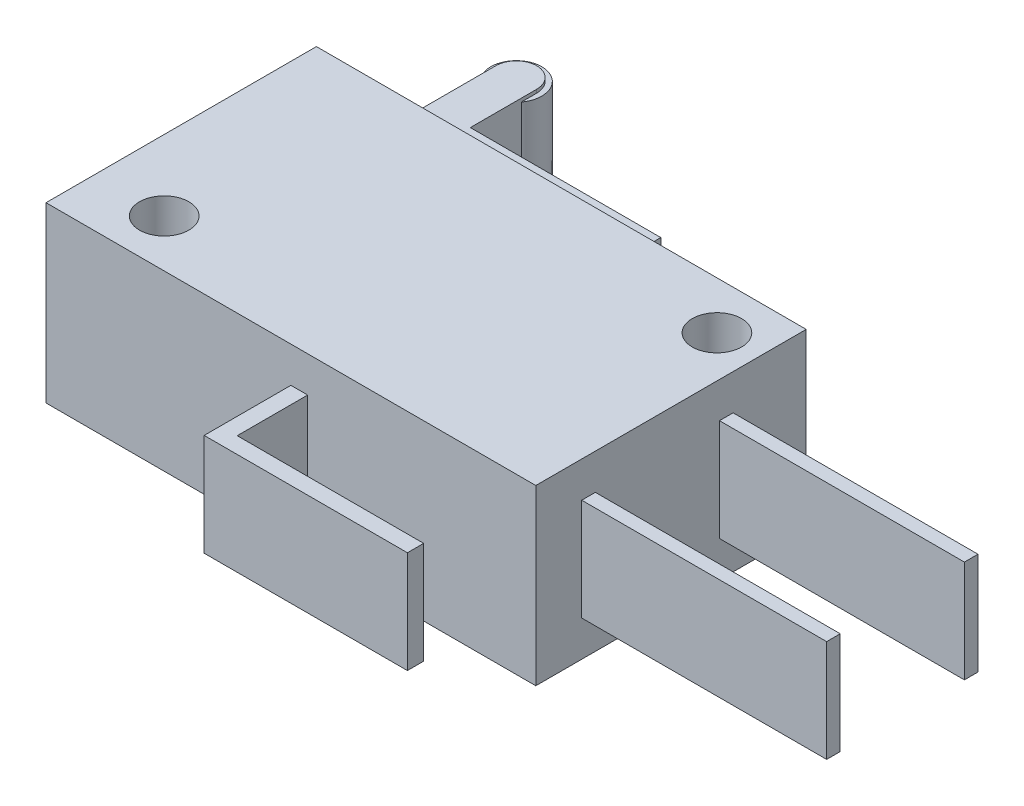
SolidWorks part; units mm, degrees
ref_plane "Front Plane" through (0, 0, 0) normal (0, 0, 1) x (1, 0, 0)
ref_plane "Top Plane" through (0, 0, 0) normal (0, 1, 0) x (1, 0, 0)
ref_plane "Right Plane" through (0, 0, 0) normal (1, 0, 0) x (0, 0, -1)
sketch "Sketch1" plane through (0, 0, 0) normal (0, 1, 0) x (1, 0, 0)
  line L5 (-14.4, -7.95) -> (14.4, -7.95)
  line L6 (-14.4, -7.95) -> (-14.4, 7.95)
  line L11 (-14.4, 7.95) -> (14.4, 7.95)
  line L12 (14.4, -7.95) -> (14.4, 7.95)
  line L13 (0, 7.95) -> (0, -7.95) construction
  line L14 (-14.4, 0) -> (14.4, 0) construction
  point P0 (0, 0)
  point P1 (0, 0)
  point P5 (0, 0)
extrude "Boss-Extrude2" add sketch "Sketch1" along normal blind 10.2
sketch "Sketch3" plane through (0, 10.2, 0) normal (0, 1, 0) x (1, 0, 0)
  line L2 (-14.4, 7.95) -> (14.4, 7.95) construction
  line L5 (14.4, -7.95) -> (14.4, 7.95) construction
  circle A0 centre (11.95, 5.15) radius 1.45
  circle A1 centre (-10.25, -5.15) radius 1.45
  point P6 (-10.3976, -4.112)
  dimension "D2" = 22.2
  dimension "D3" = 2.9
  dimension "D4" = 2.9
  dimension "D5" = 10.3
  dimension "D6" = 2.45
  dimension "D1" = 2.8
extrude "Cut-Extrude1" cut sketch "Sketch3" against normal blind 17.45
ref_plane "Plane1" through (0, 5.1, 0) normal (0, 1, 0) x (1, 0, 0)
sketch "Sketch7" plane through (0, 5.1, 0) normal (0, 1, 0) x (1, 0, 0)
  line L0 (-10.25, -5.15) -> (-10.25, 15.45) construction
  line L1 (11.95, 5.15) -> (11.95, 15.45) construction
  line L2 (11.95, 15.45) -> (-8.65, 15.45) construction
  circle A0 centre (-8.65, 13.95) radius 1.5
  dimension "D1" = 20.6
  dimension "D2" = 20.6
extrude "Boss-Extrude6" add sketch "Sketch7" against normal blind 3.2 and the other way blind 3.2 separate body
sketch "Sketch8" plane through (0, 5.1, 0) normal (0, 1, 0) x (1, 0, 0)
  line L0 (11.95, 5.15) -> (11.95, 9.6489) construction
  line L2 (-14.4, 7.95) -> (14.4, 7.95) construction
  line L4 (-9.85, 13.95) -> (-9.85, 10.05)
  line L6 (-7.45, 13.95) -> (-7.45, 10.05)
  line L11 (-7.45, 9.6489) -> (-9.85, 9.6489)
  line L14 (-9.85, 9.6489) -> (-9.85, 10.05)
  line L15 (-7.45, 10.05) -> (3.75, 10.05)
  line L17 (-8.65, 9.6489) -> (3.2389, 9.6489)
  line L18 (3.75, 10.05) -> (3.75, 9.6489)
  line L19 (3.75, 10.05) -> (3.2389, 10.05)
  line L20 (3.75, 10.05) -> (3.75, 7.95)
  line L21 (3.75, 7.95) -> (3.2389, 7.95)
  line L22 (3.2389, 9.6489) -> (3.2389, 7.95)
  arc A0 (-7.45, 13.95) -> (-9.85, 13.95) centre (-8.65, 13.95) ccw
extrude "Boss-Extrude7" add sketch "Sketch8" along normal blind 3.4 and the other way blind 3.4
sketch "Sketch9" plane through (0, 5.1, 0) normal (0, 1, 0) x (1, 0, 0)
  line L0 (14.4, -7.95) -> (14.4, 7.95) construction
  line L1 (14.4, 2.85) -> (28.8, 2.85)
  line L2 (14.4, 2.85) -> (14.4, 3.65)
  line L3 (14.4, 3.65) -> (28.8, 3.65)
  line L4 (28.8, 2.85) -> (28.8, 3.65)
  line L5 (11.95, 5.15) -> (11.95, -13.05) construction
  line L6 (14.4, -4.45) -> (28.8, -4.45)
  line L7 (14.4, -4.45) -> (14.4, -5.25)
  line L8 (14.4, -5.25) -> (28.8, -5.25)
  line L9 (28.8, -4.45) -> (28.8, -5.25)
  line L10 (0, -7.95) -> (0, -13.05)
  line L11 (-14.4, -7.95) -> (14.4, -7.95) construction
  line L12 (0, -13.05) -> (11.95, -13.05)
  line L13 (11.95, -13.05) -> (11.95, -12.0937)
  line L14 (11.95, -12.0937) -> (0.9867, -12.0937)
  line L15 (0.9867, -12.0937) -> (0.9867, -7.95)
  line L16 (0.9867, -7.95) -> (0, -7.95)
  circle A0 centre (11.95, 5.15) radius 1.45 construction
  dimension "D1" = 1.5
  dimension "D2" = 0.8
  dimension "D3" = 14.4
  dimension "D4" = 8.9
  dimension "D5" = 0.8
extrude "Boss-Extrude8" add sketch "Sketch9" along normal blind 3 and the other way blind 3
